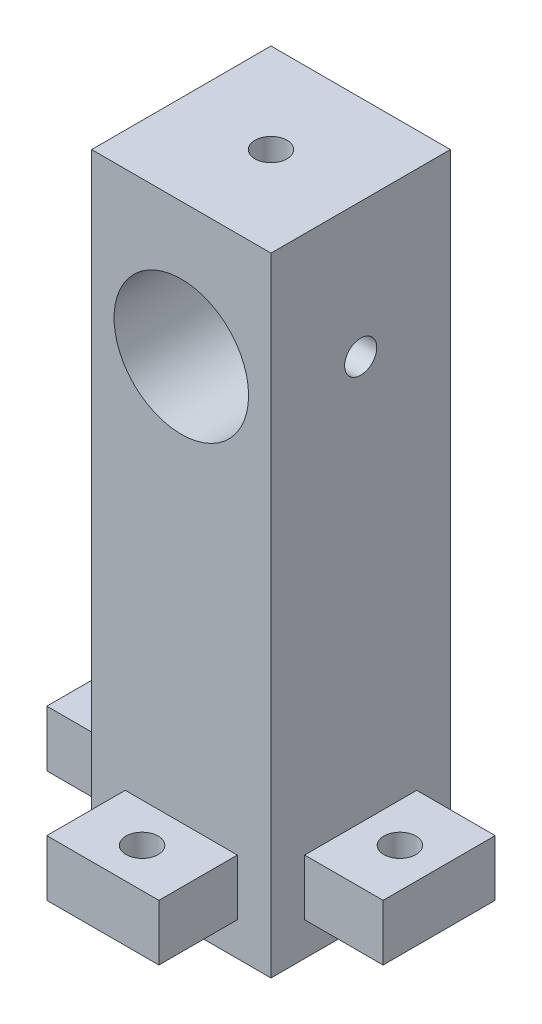
SolidWorks part; units mm, degrees
ref_plane "Alzado" through (0, 0, 0) normal (0, 0, 1) x (1, 0, 0)
ref_plane "Planta" through (0, 0, 0) normal (0, 1, 0) x (1, 0, 0)
ref_plane "Vista lateral" through (0, 0, 0) normal (1, 0, 0) x (0, 0, -1)
sketch "Croquis1" plane through (0, 0, 0) normal (0, 1, 0) x (1, 0, 0)
  line L1 (-8, 8) -> (8, 8)
  line L2 (-8, 8) -> (-8, -8)
  line L3 (-8, -8) -> (8, -8)
  line L4 (8, 8) -> (8, -8)
  line L5 (-8, 8) -> (8, -8) construction
  line L6 (-8, -8) -> (8, 8) construction
  point P0 (0, 0)
  dimension "D1" = 16
  dimension "D2" = 16
extrude "Saliente-Extruir1" add sketch "Croquis1" along normal blind 56
sketch "Croquis2" plane through (0, 0, 8) normal (0, 0, 1) x (1, 0, 0)
  line L0 (-8, 56) -> (8, 56) construction
  line L1 (8, 56) -> (8, 0) construction
  circle A0 centre (0, 44) radius 6
  dimension "D1" = 12
  dimension "D2" = 12
  dimension "D3" = 8
extrude "Cortar-Extruir1" cut sketch "Croquis2" against normal up to next
sketch "Croquis3" plane through (8, 0, 0) normal (1, 0, 0) x (0, 0, -1)
  line L0 (8, 56) -> (8, 0) construction
  line L2 (-8, 56) -> (8, 56) construction
  circle A0 centre (0, 44) radius 1.435
  dimension "D3" = 2.87
  dimension "D1" = 8
  dimension "D2" = 12
extrude "Cortar-Extruir2" cut sketch "Croquis3" against normal blind 16
sketch "Croquis4" plane through (0, 56, 0) normal (0, 1, 0) x (1, 0, 0)
  circle A0 centre (0, 0) radius 1.435
  dimension "D1" = 2.87
extrude "Cortar-Extruir3" cut sketch "Croquis4" against normal up to next
sketch "Croquis5" plane through (-8, 0, 0) normal (-1, 0, 0) x (0, 0, 1)
  line L1 (5, 3) -> (-5, 3)
  line L2 (5, 3) -> (5, 8)
  line L3 (5, 8) -> (-5, 8)
  line L4 (-5, 3) -> (-5, 8)
  line L5 (8, 56) -> (8, 0) construction
  line L6 (-8, 0) -> (8, 0) construction
  dimension "D1" = 5
  dimension "D2" = 10
  dimension "D3" = 3
  dimension "D4" = 8
extrude "Saliente-Extruir2" add sketch "Croquis5" along normal blind 7
sketch "Croquis6" plane through (0, 8, 0) normal (0, 1, 0) x (1, 0, 0)
  line L0 (-8, -5) -> (-8, 5) construction
  line L1 (-15, -5) -> (-8, -5) construction
  circle A0 centre (-11.5, 0) radius 1.435
  dimension "D1" = 2.87
  dimension "D2" = 3.5
  dimension "D3" = 5
extrude "Cortar-Extruir4" cut sketch "Croquis6" against normal up to next (5 mm away) contours A0
mirror "Simetría1" about plane through (0, 0, 0) normal (1, 0, 0) of "Saliente-Extruir2", "Cortar-Extruir4"
sketch "Croquis7" plane through (0, 0, 8) normal (0, 0, 1) x (1, 0, 0)
  line L0 (-8, 3) -> (-8, 8) construction
  line L1 (5, 3) -> (-5, 3)
  line L2 (5, 3) -> (5, 8)
  line L3 (5, 8) -> (-5, 8)
  line L4 (-5, 3) -> (-5, 8)
  line L5 (-8, 0) -> (8, 0) construction
  dimension "D1" = 10
  dimension "D2" = 3
  dimension "D3" = 3
  dimension "D4" = 5
extrude "Saliente-Extruir3" add sketch "Croquis7" along normal blind 7
sketch "Croquis8" plane through (0, 8, 0) normal (0, 1, 0) x (1, 0, 0)
  line L0 (5, -8) -> (-5, -8) construction
  line L1 (5, -15) -> (5, -8) construction
  circle A0 centre (0, -11.5) radius 1.435
  dimension "D3" = 2.87
  dimension "D1" = 3.5
  dimension "D2" = 5
extrude "Cortar-Extruir5" cut sketch "Croquis8" against normal up to next
